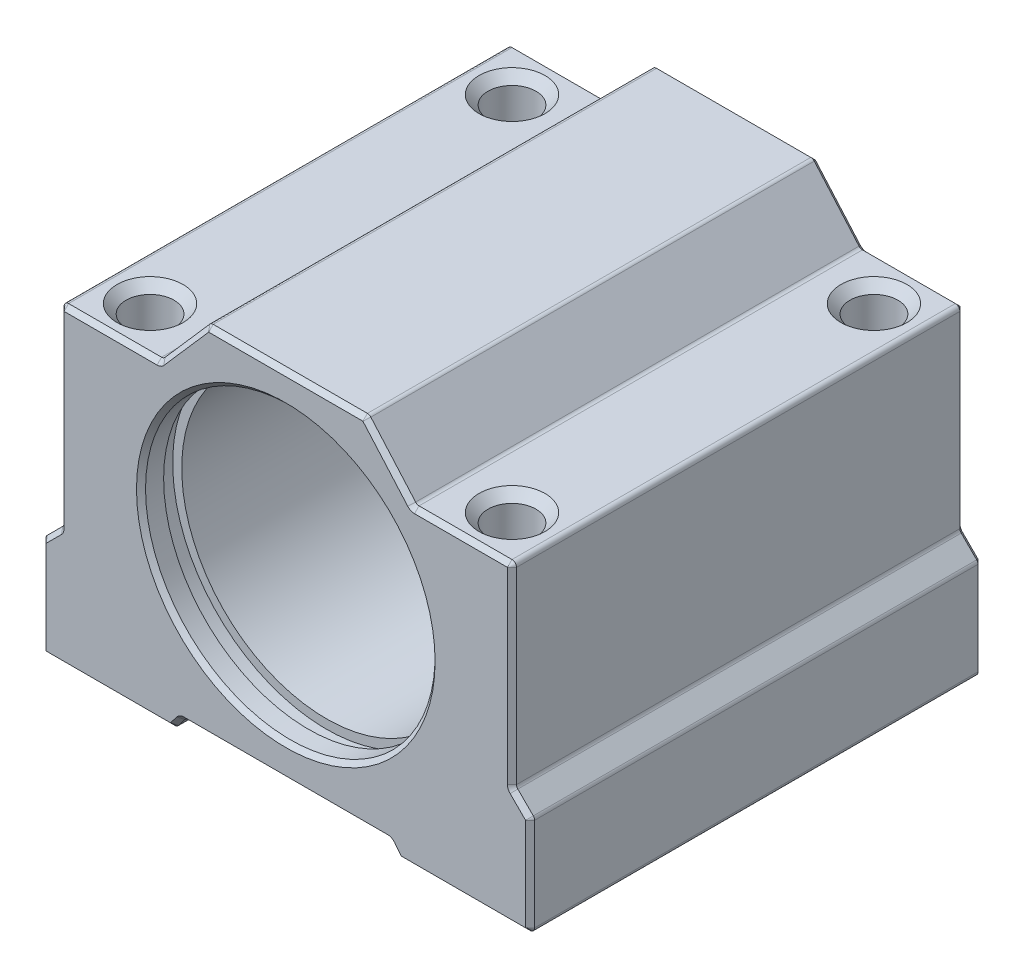
SolidWorks part; units mm, degrees
material "Сплав 1060"
ref_plane "Спереди" through (0, 0, 0) normal (0, 0, 1) x (1, 0, 0)
ref_plane "Сверху" through (0, 0, 0) normal (0, 1, 0) x (1, 0, 0)
ref_plane "Справа" through (0, 0, 0) normal (1, 0, 0) x (0, 0, -1)
sketch "Эскиз1" plane through (0, 0, 0) normal (0, 0, 1) x (1, 0, 0)
  line L1 (-25, -20.25) -> (25, -20.25)
  line L2 (-25, -20.25) -> (-25, 20.25)
  line L3 (-25, 20.25) -> (25, 20.25)
  line L4 (25, -20.25) -> (25, 20.25)
  line L5 (-25, -20.25) -> (25, 20.25) construction
  line L6 (-25, 20.25) -> (25, -20.25) construction
  point P0 (0, 0)
  dimension "D1" = 40.5
  dimension "D2" = 50
extrude "Бобышка-Вытянуть1" add sketch "Эскиз1" along normal mid plane 50
sketch "Эскиз5" plane through (0, 20.25, 0) normal (0, 1, 0) x (1, 0, 0)
  line L1 (-20, -20) -> (20, -20) construction
  line L2 (-20, -20) -> (-20, 20) construction
  line L3 (-20, 20) -> (20, 20) construction
  line L4 (20, -20) -> (20, 20) construction
  line L5 (-20, -20) -> (20, 20) construction
  line L6 (-20, 20) -> (20, -20) construction
  circle A0 centre (-20, 20) radius 2.65
  circle A1 centre (20, 20) radius 2.65
  circle A2 centre (20, -20) radius 2.65
  circle A3 centre (-20, -20) radius 2.65
  point P0 (0, 0)
  dimension "D1" = 5.3
  dimension "D2" = 40
  dimension "D3" = 40
extrude "Вырез-Вытянуть2" cut sketch "Эскиз5" against normal through all
sketch "Эскиз6" plane through (0, 0, 25) normal (0, 0, 1) x (1, 0, 0)
  line L0 (-25, 14.25) -> (-14, 14.25)
  line L1 (-25, 20.25) -> (-25, -20.25) construction
  line L2 (-14, 14.25) -> (-8.75, 20.25)
  line L3 (25, 20.25) -> (-25, 20.25) construction
  line L4 (-8.75, 20.25) -> (-25, 20.25)
  line L5 (-25, 20.25) -> (-25, 14.25)
  line L6 (25, 20.25) -> (25, 14.25)
  line L7 (25, -20.25) -> (25, 20.25) construction
  line L8 (25, 14.25) -> (14, 14.25)
  line L9 (14, 14.25) -> (8.75, 20.25)
  line L10 (8.75, 20.25) -> (25, 20.25)
  dimension "D1" = 17.5
  dimension "D2" = 6
  dimension "D3" = 28
extrude "Вырез-Вытянуть3" cut sketch "Эскиз6" against normal up to next
sketch "Эскиз7" plane through (0, 0, 25) normal (0, 0, 1) x (1, 0, 0)
  line L0 (-12.5, -20.25) -> (-11.5, -18.95)
  line L1 (-25, -20.25) -> (25, -20.25) construction
  line L2 (-11.5, -18.95) -> (11.5, -18.95)
  line L3 (11.5, -18.95) -> (12.5, -20.25)
  line L4 (12.5, -20.25) -> (-12.5, -20.25)
  point P4 (0, -4)
  point P7 (0, -18.95)
  dimension "D1" = 25
  dimension "D2" = 23
  dimension "D3" = 1.3
extrude "Вырез-Вытянуть4" cut sketch "Эскиз7" against normal through all
sketch "Эскиз8" plane through (0, 0, 25) normal (0, 0, 1) x (1, 0, 0)
  line L0 (25, -20.25) -> (27, -20.25)
  line L1 (27, -20.25) -> (27, -9.25)
  line L2 (27, -9.25) -> (25, -7.25)
  line L3 (25, -20.25) -> (25, 14.25) construction
  line L4 (25, -7.25) -> (25, -20.25)
  line L5 (-25, -20.25) -> (-25, -7.25)
  line L6 (-25, 14.25) -> (-25, -20.25) construction
  line L7 (-25, -7.25) -> (-27, -9.25)
  line L8 (-27, -9.25) -> (-27, -20.25)
  line L9 (-27, -20.25) -> (-25, -20.25)
  dimension "D1" = 54
  dimension "D2" = 11
extrude "Бобышка-Вытянуть2" add sketch "Эскиз8" against normal up to surface (50 mm away) up to face at (0, -1.7833, -25)
chamfer "Фаска1" distance 1 angle 45 8 edges at (-17.35, 14.25, 20) (-17.35, 14.25, -20) (22.65, 14.25, 20) (22.65, 14.25, -20) (20, -20.25, 22.65) (20, -20.25, -17.35) (-20, -20.25, -17.35) (-20, -20.25, 22.65)
sketch "Эскиз9" plane through (0, -20.25, 0) normal (0, -1, 0) x (1, 0, 0)
  circle A0 centre (-20, 20) radius 3
  circle A1 centre (20, 20) radius 3
  circle A2 centre (20, -20) radius 3
  circle A3 centre (-20, -20) radius 3
  dimension "D1" = 6
extrude "M6x12" cut sketch "Эскиз9" against normal blind 12
fillet "Скругление1" radius 0.5 16 edges at (-27, -9.25, 0) (-27, -20.25, 0) (-12.5, -20.25, 0) (-11.5, -18.95, 0) (11.5, -18.95, 0) (12.5, -20.25, 0) (27, -20.25, 0) (27, -9.25, 0) (-25, 14.25, 0) (-14, 14.25, 0) (-8.75, 20.25, 0) (8.75, 20.25, 0) (14, 14.25, 0) (25, 14.25, 0)
chamfer "Фаска3" distance 0.5 angle 45 64 edges at (0, -18.95, -25) (11.4747, -19.0014, -25) (-11.4747, -19.0014, -25) (12, -19.6, -25) (-12, -19.6, -25) (12.5253, -20.1986, -25) (-12.5253, -20.1986, -25) (19.6231, -20.25, -25) (-19.6231, -20.25, -25) (26.8536, -20.1036, -25) (-26.8536, -20.1036, -25) (27, -14.6036, 25) (27, -14.6036, -25) (-27, -14.6036, 25) (-27, -14.6036, -25) (26.9619, -9.2658, -25) (-26.9619, -9.2658, -25) (25.0381, -7.2342, -25) (-25.0381, -7.2342, -25) (24.8536, 14.1036, -25) (-24.8536, 14.1036, -25) (19.3634, 14.25, -25) (-19.3634, 14.25, -25) (14.0203, 14.2947, -25) (-14.0203, 14.2947, -25) (11.375, 17.25, -25) (-11.375, 17.25, -25) (8.7297, 20.2053, -25) (-8.7297, 20.2053, -25) (0, 20.25, -25) (0, -18.95, 25) (11.4747, -19.0014, 25) (-11.4747, -19.0014, 25) (12, -19.6, 25) (-12, -19.6, 25) (12.5253, -20.1986, 25) (-12.5253, -20.1986, 25) (19.6231, -20.25, 25) (-19.6231, -20.25, 25) (26.8536, -20.1036, 25) (-26.8536, -20.1036, 25) (26.9619, -9.2658, 25) (-26.9619, -9.2658, 25) (25.0381, -7.2342, 25) (-25.0381, -7.2342, 25) (24.8536, 14.1036, 25) (-24.8536, 14.1036, 25) (19.3634, 14.25, 25) (-19.3634, 14.25, 25) (14.0203, 14.2947, 25) (-14.0203, 14.2947, 25) (11.375, 17.25, 25) (-11.375, 17.25, 25) (8.7297, 20.2053, 25) (-8.7297, 20.2053, 25) (0, 20.25, 25)
sketch "Эскиз10" plane through (0, 0, 25) normal (0, 0, 1) x (1, 0, 0)
  line L2 (26.5, -20.25) -> (12.7462, -20.25) construction
  circle A0 centre (0, 0.75) radius 16
  dimension "D1" = 32
  dimension "D2" = 21
extrude "Вырез-Вытянуть6" cut sketch "Эскиз10" against normal up to next
chamfer "Фаска4" distance 0.5 angle 45 2 edges at (16, 0.75, 25) (-16, 0.75, -25)
sketch "Эскиз11" plane through (0, 0, 0) normal (1, 0, 0) x (0, 0, -1)
  line L0 (-25, 0.75) -> (25, 0.75) construction
  line L1 (-25, 17.25) -> (-25, -15.75) construction
  line L2 (25, -15.75) -> (25, 17.25) construction
  line L3 (-22.5, 0.75) -> (-22.5, 17.75)
  line L4 (-22.5, 17.75) -> (-20.5, 17.75)
  line L5 (-20.5, 17.75) -> (-20.5, 0.75)
  line L6 (-20.5, 0.75) -> (-22.5, 0.75)
  line L7 (20.5, 0.75) -> (20.5, 17.75)
  line L8 (20.5, 17.75) -> (22.5, 17.75)
  line L9 (22.5, 17.75) -> (22.5, 0.75)
  line L10 (22.5, 0.75) -> (20.5, 0.75)
  line L11 (-20.5, 17.75) -> (20.5, 17.75) construction
  line L12 (0, 0) -> (0, 17.75) construction
  dimension "D1" = 4.5
  dimension "D2" = 2
  dimension "D3" = 17
revolve "Вырез-Повернуть1" cut sketch "Эскиз11" angle 360 about L0
